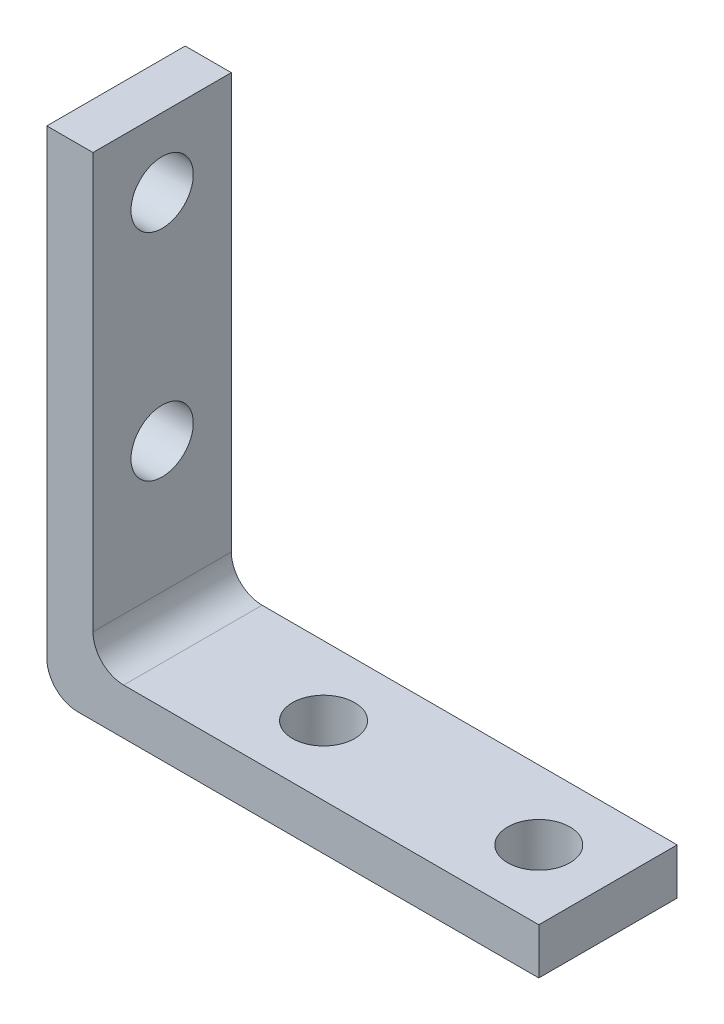
SolidWorks part; units mm, degrees
material "1060 合金"
ref_plane "前视基准面" through (0, 0, 0) normal (0, 0, 1) x (1, 0, 0)
ref_plane "上视基准面" through (0, 0, 0) normal (0, 1, 0) x (1, 0, 0)
ref_plane "右视基准面" through (0, 0, 0) normal (1, 0, 0) x (0, 0, -1)
other "Configuration Table"
sketch "草图1" plane through (0, 0, 0) normal (0, 0, 1) x (1, 0, 0)
  line L1 (0, 0) -> (32, 0)
  line L2 (0, 0) -> (0, 3)
  line L3 (0, 3) -> (32, 3)
  line L4 (32, 0) -> (32, 3)
  line L5 (0, 3) -> (3, 3)
  line L6 (0, 3) -> (0, 32)
  line L7 (0, 32) -> (3, 32)
  line L8 (3, 3) -> (3, 32)
  dimension "D1" = 3
  dimension "D2" = 32
  dimension "D3" = 32
extrude "凸台-拉伸1" add sketch "草图1" along normal mid plane 9 contours L3 L8 L7 L6 | L1 L4 L3 L2
sketch "草图3" plane through (0, 0, 0) normal (0, -1, 0) x (1, 0, 0)
  line L0 (0, 0) -> (50000, 0) construction
  line L1 (0, 4.5) -> (0, -4.5) construction
  line L2 (32, 4.5) -> (32, -4.5) construction
  circle A0 centre (13.5, 0) radius 2.025
  circle A1 centre (27.5, 0) radius 2.025
  point P4 (0, 0)
  dimension "D1" = 14
  dimension "D2" = 4.05
  dimension "D3" = 4.5
extrude "切除-拉伸1" cut sketch "草图3" against normal blind 9
sketch "草图4" plane through (0, 0, 0) normal (-1, 0, 0) x (0, 0, 1)
  line L0 (0, 27.5) -> (0, 13.5) construction
  line L1 (0, 13.5) -> (0, 0) construction
  line L2 (4.5, 32) -> (-4.5, 32) construction
  circle A0 centre (0, 27.5) radius 2.025
  circle A1 centre (0, 13.5) radius 2.025
  dimension "D1" = 4.05
  dimension "D3" = 4.5
  dimension "D2" = 14
extrude "切除-拉伸2" cut sketch "草图4" against normal blind 9
fillet "圆角1" radius 2 2 edges at (3, 3, 0) (0, 0, 0)
